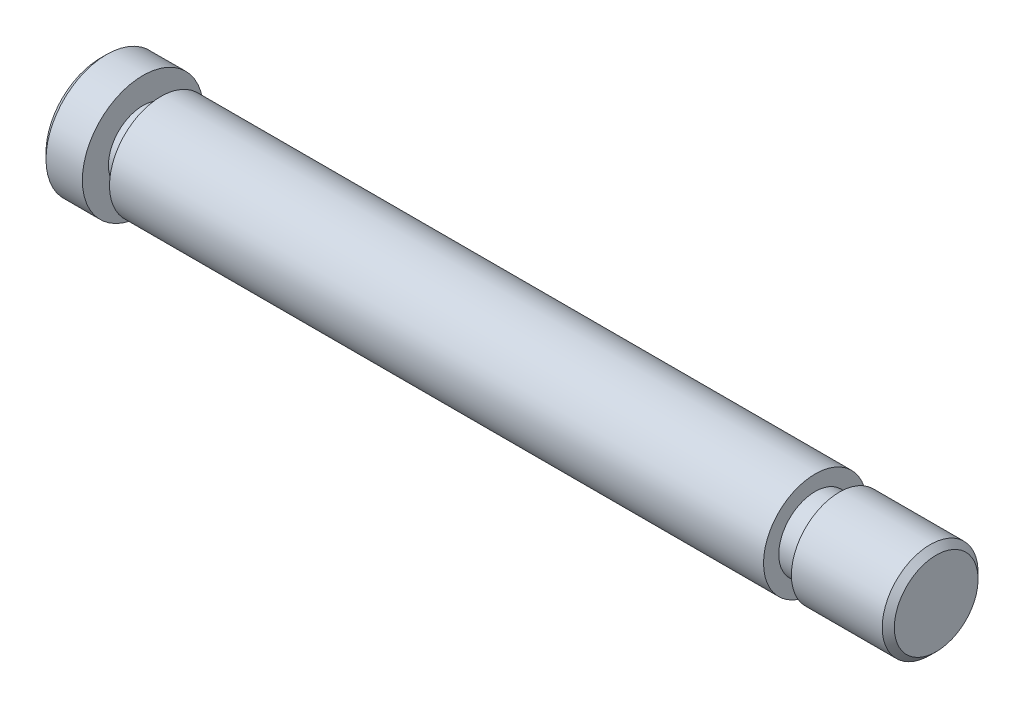
SolidWorks part; units mm, degrees
ref_plane "Front Plane" through (0, 0, 0) normal (0, 0, 1) x (1, 0, 0)
ref_plane "Top Plane" through (0, 0, 0) normal (0, 1, 0) x (1, 0, 0)
ref_plane "Right Plane" through (0, 0, 0) normal (1, 0, 0) x (0, 0, -1)
sketch "Sketch1" plane through (0, 0, 0) normal (0, 0, 1) x (1, 0, 0)
  line L0 (-14.9704, 0) -> (22.2949, 0) construction
  line L1 (-8.5234, 1.5) -> (-8.5234, 5)
  line L2 (-8.5234, 5) -> (-5.0234, 5)
  line L3 (-5.0234, 5) -> (-5.0234, 2.8461)
  line L4 (-5.0234, 2.8461) -> (-3.5234, 2.8461)
  line L5 (-3.5234, 2.8461) -> (-3.5234, 4.2577)
  line L6 (-3.5234, 4.2577) -> (50.4766, 4.2577)
  line L7 (50.4766, 4.2577) -> (50.4766, 3)
  line L8 (50.4766, 3) -> (52.4766, 3)
  line L9 (52.4766, 3) -> (52.4766, 3.9564)
  line L10 (52.4766, 3.9564) -> (60.4766, 3.9564)
  line L11 (60.4766, 3.9564) -> (60.4766, 0)
  line L12 (-8.5234, 1.5) -> (16.9766, 1.5)
  line L13 (16.9766, 1.5) -> (16.9766, 0)
  line L14 (16.9766, 0) -> (60.4766, 0)
  point P11 (50.4766, 3.6288)
  point P16 (-8.5234, 3.25)
  dimension "D1" = 5
  dimension "D2" = 3
  dimension "D3" = 2
  dimension "D4" = 10
  dimension "D5" = 69
  dimension "D6" = 5
  dimension "D7" = 1.5
  dimension "D8" = 25.5
  dimension "D9" = 1.5
revolve "Revolve1" add sketch "Sketch1" angle 360 about L0
chamfer "Chamfer1" distance 0.5 angle 45 1 edges at (-8.5234, 0, 5)
chamfer "Chamfer2" distance 0.5 angle 45 1 edges at (60.4766, 0, 3.9564)
